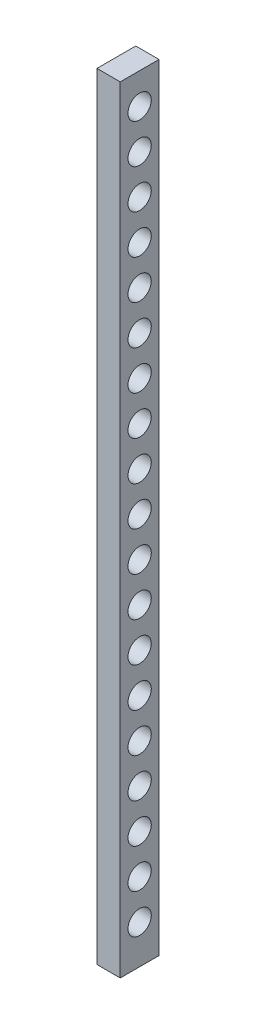
SolidWorks part; units mm, degrees
ref_plane "前视基准面" through (0, 0, 0) normal (0, 0, 1) x (1, 0, 0)
ref_plane "上视基准面" through (0, 0, 0) normal (0, 1, 0) x (1, 0, 0)
ref_plane "右视基准面" through (0, 0, 0) normal (1, 0, 0) x (0, 0, -1)
sketch "草图1" plane through (0, 0, 0) normal (1, 0, 0) x (0, 0, -1)
  line L0 (0, 0) -> (4.4697, 0) construction
  line L1 (0, 0) -> (0, 5.2195) construction
  line L2 (5, 0) -> (5, -200)
  line L3 (0, 0) -> (10, 0)
  line L4 (0, 0) -> (0, -200)
  line L5 (0, -200) -> (10, -200)
  line L6 (10, 0) -> (10, -200)
  circle A0 centre (5, -7.9981) radius 3
  circle A20 centre (5, -18.1092) radius 3
  circle A21 centre (5, -28.2202) radius 3
  circle A22 centre (5, -38.3312) radius 3
  circle A23 centre (5, -48.4422) radius 3
  circle A24 centre (5, -58.5533) radius 3
  circle A25 centre (5, -68.6643) radius 3
  circle A26 centre (5, -78.7753) radius 3
  circle A27 centre (5, -88.8863) radius 3
  circle A28 centre (5, -98.9973) radius 3
  circle A29 centre (5, -109.1084) radius 3
  circle A30 centre (5, -119.2194) radius 3
  circle A31 centre (5, -129.3304) radius 3
  circle A32 centre (5, -139.4414) radius 3
  circle A33 centre (5, -149.5525) radius 3
  circle A34 centre (5, -159.6635) radius 3
  circle A35 centre (5, -169.7745) radius 3
  circle A36 centre (5, -179.8855) radius 3
  circle A37 centre (5, -189.9965) radius 3
  circle A38 centre (15, -7.9981) radius 3 [skipped]
  circle A39 centre (15, -18.1092) radius 3 [skipped]
  circle A40 centre (15, -28.2202) radius 3 [skipped]
  circle A41 centre (15, -38.3312) radius 3 [skipped]
  circle A42 centre (15, -48.4422) radius 3 [skipped]
  circle A43 centre (15, -58.5533) radius 3 [skipped]
  circle A44 centre (15, -68.6643) radius 3 [skipped]
  circle A45 centre (15, -78.7753) radius 3 [skipped]
  circle A46 centre (15, -88.8863) radius 3 [skipped]
  circle A47 centre (15, -98.9973) radius 3 [skipped]
  circle A48 centre (15, -109.1084) radius 3 [skipped]
  circle A49 centre (15, -119.2194) radius 3 [skipped]
  circle A50 centre (15, -129.3304) radius 3 [skipped]
  circle A51 centre (15, -139.4414) radius 3 [skipped]
  circle A52 centre (15, -149.5525) radius 3 [skipped]
  circle A53 centre (15, -159.6635) radius 3 [skipped]
  circle A54 centre (15, -169.7745) radius 3 [skipped]
  circle A55 centre (15, -179.8855) radius 3 [skipped]
  circle A56 centre (15, -189.9965) radius 3 [skipped]
  dimension "D3" = 2
  dimension "D4" = 19
extrude "凸台-拉伸1" add sketch "草图1" along normal blind 6 contours A37 L2 A36 A35 A34 A33 A32 A31 A30 A29 A28 A27 A26 A25 A24 A23 A22 A21 A20 A0 L3 L4 L5 | A37 L2 L5 L6 L3 A0 A20 A21 A22 A23 A24 A25 A26 A27 A28 A29 A30 A31 A32 A33 A34 A35 A36
